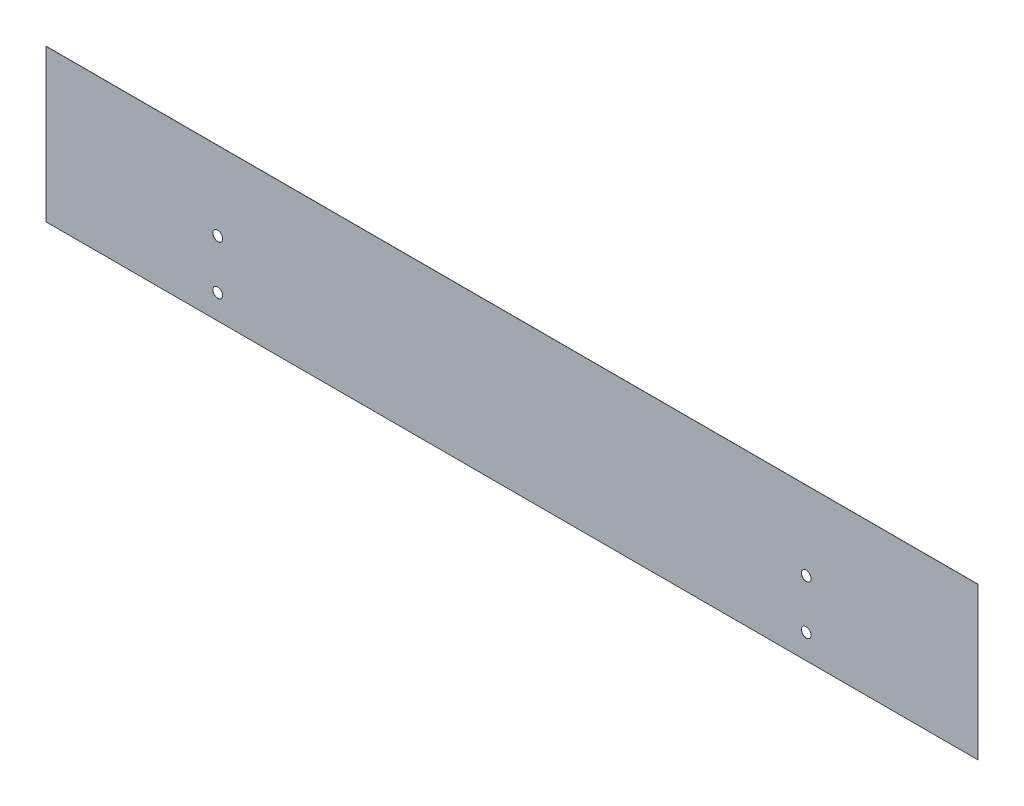
SolidWorks part; units mm, degrees
ref_plane "Front Plane" through (0, 0, 0) normal (0, 0, 1) x (1, 0, 0)
ref_plane "Top Plane" through (0, 0, 0) normal (0, 1, 0) x (1, 0, 0)
ref_plane "Right Plane" through (0, 0, 0) normal (1, 0, 0) x (0, 0, -1)
sketch "Sketch1" plane through (0, 0, 0) normal (0, 0, 1) x (1, 0, 0)
  line L1 (-190, -31) -> (190, -31)
  line L2 (-190, -31) -> (-190, 31)
  line L3 (-190, 31) -> (190, 31)
  line L4 (190, -31) -> (190, 31)
  line L5 (-190, -31) -> (190, 31) construction
  line L6 (-190, 31) -> (190, -31) construction
  point P0 (0, 0)
  dimension "D1" = 380
  dimension "D2" = 62
extrude "Body" add sketch "Sketch1" along normal blind 0.0625
sketch "Sketch2" plane through (0, 0, 0.0625) normal (0, 0, 1) x (1, 0, 0)
  line L0 (-120, -21) -> (120, -21) construction
  line L1 (120, -21) -> (120, -1) construction
  line L2 (120, -1) -> (-120, -1) construction
  line L3 (-120, -1) -> (-120, -21) construction
  line L4 (0, -1) -> (0, -21) construction
  line L6 (-190, -31) -> (190, -31) construction
  line L7 (-190, 31) -> (-190, -31) construction
  circle A0 centre (-120, -1) radius 2
  circle A1 centre (120, -1) radius 2
  circle A2 centre (120, -21) radius 2
  circle A3 centre (-120, -21) radius 2
  point P10 (0, -11)
  point P14 (3.5603, -10.0714)
  dimension "D1" = 4
  dimension "D2" = 20
  dimension "D3" = 10
  dimension "D4" = 70
extrude "Magnetic Holder" cut sketch "Sketch2" against normal blind 0.0625
